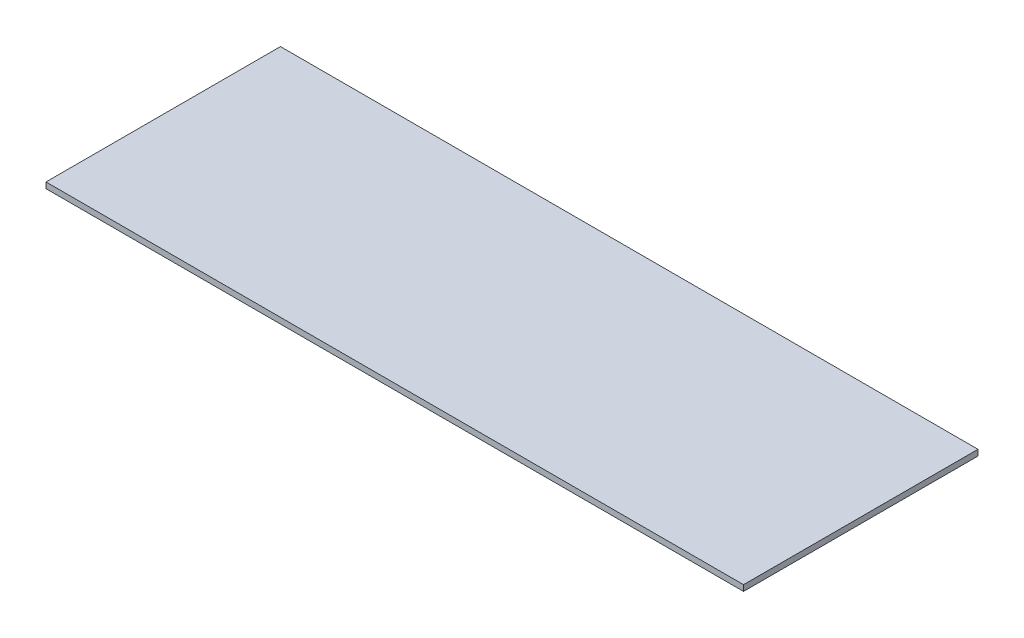
SolidWorks part; units mm, degrees
ref_plane "Front Plane" through (0, 0, 0) normal (0, 0, 1) x (1, 0, 0)
ref_plane "Top Plane" through (0, 0, 0) normal (0, 1, 0) x (1, 0, 0)
ref_plane "Right Plane" through (0, 0, 0) normal (1, 0, 0) x (0, 0, -1)
sketch "Sketch1" plane through (0, 0, 0) normal (0, 1, 0) x (1, 0, 0)
  line L1 (-755.65, -254) -> (755.65, -254)
  line L2 (-755.65, -254) -> (-755.65, 254)
  line L3 (-755.65, 254) -> (755.65, 254)
  line L4 (755.65, -254) -> (755.65, 254)
  line L5 (-755.65, -254) -> (755.65, 254) construction
  line L6 (-755.65, 254) -> (755.65, -254) construction
  point P0 (0, 0)
  dimension "D1" = 1511.3
  dimension "D2" = 508
extrude "Boss-Extrude1" add sketch "Sketch1" along normal blind 12.7
